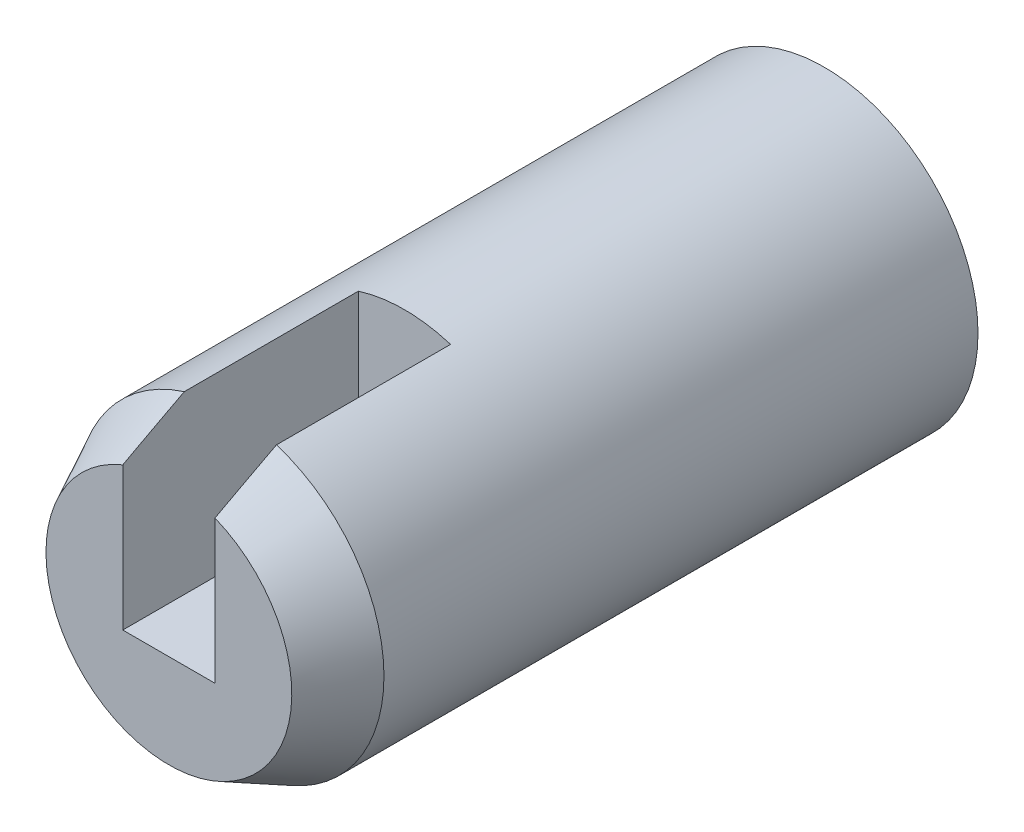
SolidWorks part; units mm, degrees
ref_plane "Plan de face" through (0, 0, 0) normal (0, 0, 1) x (1, 0, 0)
ref_plane "Plan de dessus" through (0, 0, 0) normal (0, 1, 0) x (1, 0, 0)
ref_plane "Plan de droite" through (0, 0, 0) normal (1, 0, 0) x (0, 0, -1)
sketch "Esquisse1" plane through (0, 0, 0) normal (0, 0, 1) x (1, 0, 0)
  circle A1 centre (-15.7706, 6.5298) radius 7.5
  dimension "D1" = 15
extrude "Boss.-Extru.2" add sketch "Esquisse1" along normal blind 29 contours A1
ref_plane "Plan2" through (0, 0, 32) normal (0, 0, 1) x (1, 0, 0)
sketch "Esquisse10" plane through (0, 0, 32) normal (0, 0, 1) x (1, 0, 0)
  circle A1 centre (-15.7706, 6.5298) radius 6
  dimension "D1" = 12
loft "Lissage3" add profiles "Esquisse10" section edge at (-8.2706, 6.5298, 29) section "Esquisse10"
sketch "Esquisse11" plane through (0, 0, 0) normal (0, 0, -1) x (-1, 0, 0)
  circle A0 centre (15.7706, 6.5298) radius 6
  dimension "D1" = 12
extrude "Enlèv. mat.-Extru.1" cut sketch "Esquisse11" against normal blind 8
sketch "Esquisse13" plane through (0, 0, 32) normal (0, 0, 1) x (1, 0, 0)
  line L0 (-15.7706, 5.1072) -> (-18.0206, 5.1072)
  line L1 (-18.0206, 5.1072) -> (-18.0206, 15.8962)
  line L2 (-18.0206, 15.8962) -> (-13.5206, 15.8962)
  line L3 (-13.5206, 15.8962) -> (-13.5206, 5.1072)
  line L4 (-13.5206, 5.1072) -> (-15.7706, 5.1072)
  point P3 (0, 0)
  point P7 (0, 0)
  dimension "D1" = 2.25
  dimension "D2" = 2.25
  dimension "D3" = 4.5
extrude "Enlèv. mat.-Extru.2" cut sketch "Esquisse13" against normal blind 11.5
